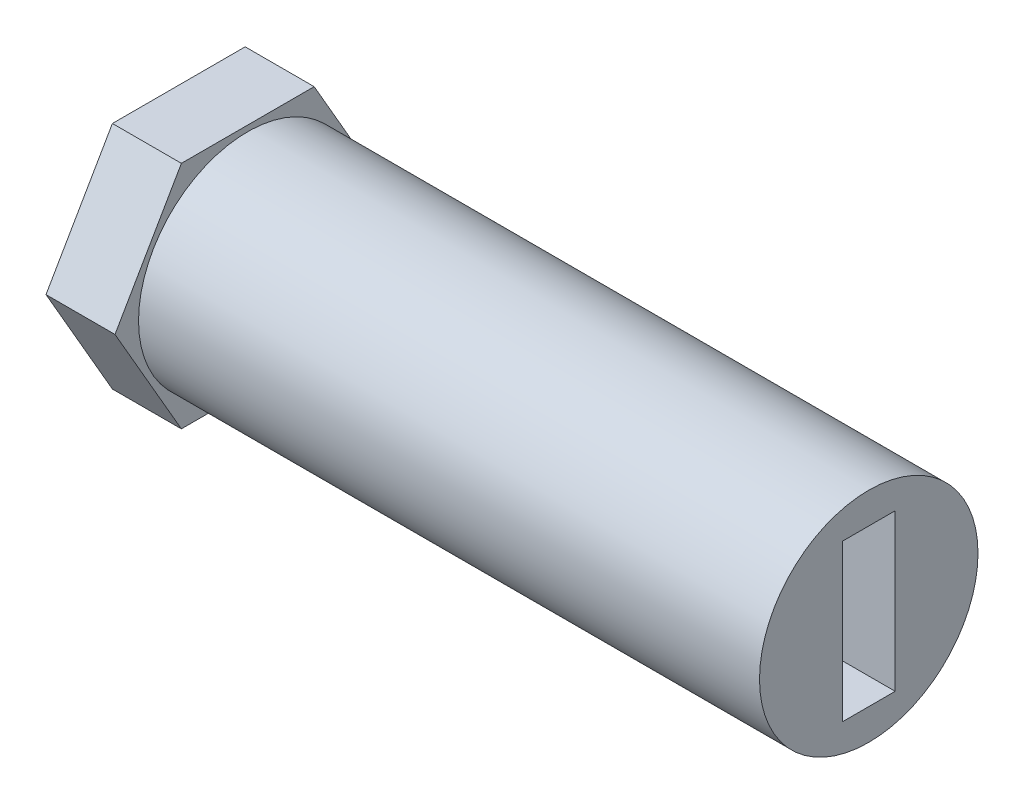
SolidWorks part; units mm, degrees
ref_plane "Front Plane" through (0, 0, 0) normal (0, 0, 1) x (1, 0, 0)
ref_plane "Top Plane" through (0, 0, 0) normal (0, 1, 0) x (1, 0, 0)
ref_plane "Right Plane" through (0, 0, 0) normal (1, 0, 0) x (0, 0, -1)
sketch "Sketch1" plane through (0, 0, 0) normal (1, 0, 0) x (0, 0, -1)
  circle A0 centre (0, 0) radius 4.75
  dimension "D1" = 9.5
extrude "Boss-Extrude1" add sketch "Sketch1" along normal blind 30
sketch "Sketch2" plane through (30, 0, 0) normal (1, 0, 0) x (0, 0, -1)
  line L1 (-1.15, -3.4) -> (1.15, -3.4)
  line L2 (-1.15, -3.4) -> (-1.15, 3.4)
  line L3 (-1.15, 3.4) -> (1.15, 3.4)
  line L4 (1.15, -3.4) -> (1.15, 3.4)
  line L5 (-1.15, -3.4) -> (1.15, 3.4) construction
  line L6 (-1.15, 3.4) -> (1.15, -3.4) construction
  point P0 (0, 0)
  dimension "D1" = 2.3
  dimension "D2" = 6.8
extrude "Cut-Extrude1" cut sketch "Sketch2" against normal up to surface (30 mm away) up to face at (0, 0, -4.75)
sketch "Sketch3" plane through (0, 0, 0) normal (-1, 0, 0) x (0, 0, 1)
  line L1 (5.7735, 0) -> (2.8868, 5)
  line L2 (2.8868, 5) -> (-2.8868, 5)
  line L3 (-2.8868, 5) -> (-5.7735, 0)
  line L4 (-5.7735, 0) -> (-2.8868, -5)
  line L5 (-2.8868, -5) -> (2.8868, -5)
  line L6 (2.8868, -5) -> (5.7735, 0)
  circle A0 centre (0, 0) radius 5 construction
extrude "Boss-Extrude2" add sketch "Sketch3" against normal blind 3
